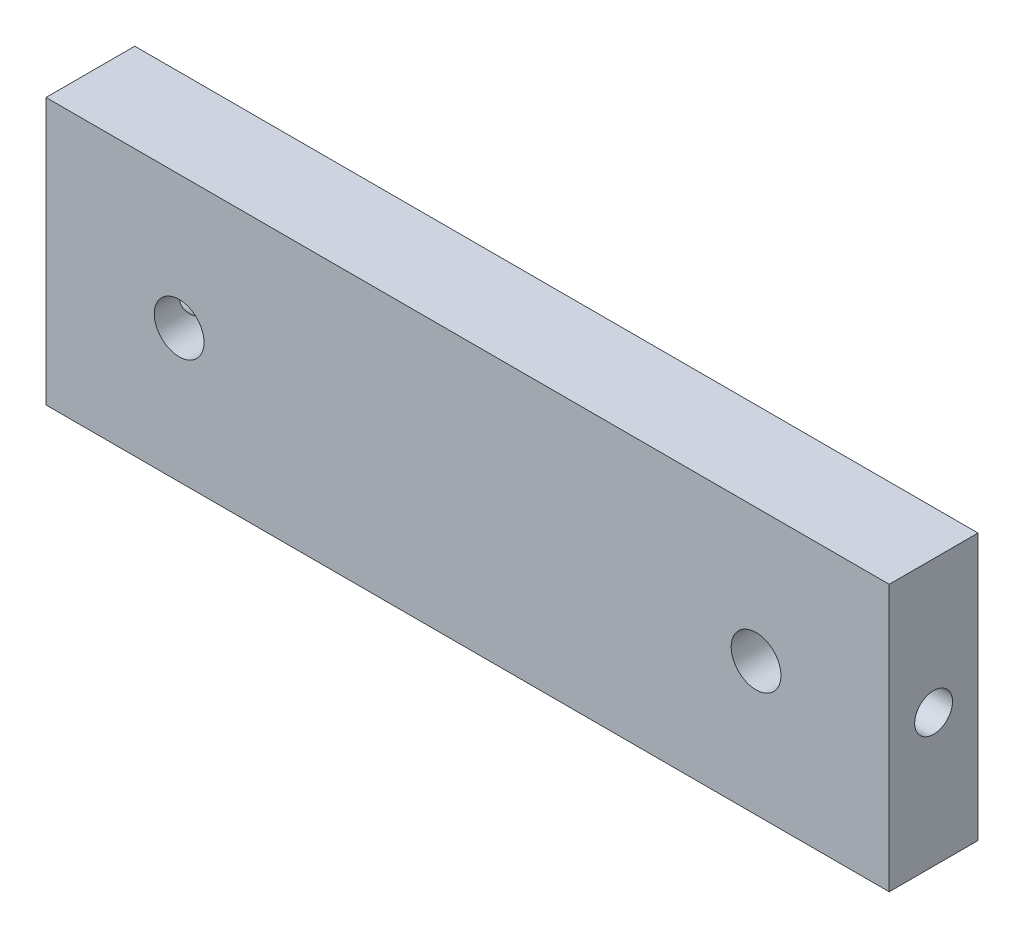
SolidWorks part; units mm, degrees
ref_plane "Front Plane" through (0, 0, 0) normal (0, 0, 1) x (1, 0, 0)
ref_plane "Top Plane" through (0, 0, 0) normal (0, 1, 0) x (1, 0, 0)
ref_plane "Right Plane" through (0, 0, 0) normal (1, 0, 0) x (0, 0, -1)
sketch "Sketch1" plane through (0, 0, 0) normal (0, 0, 1) x (1, 0, 0)
  line L1 (0, 0) -> (60.3123, 0)
  line L2 (0, 0) -> (0, 19.05)
  line L3 (0, 19.05) -> (60.3123, 19.05)
  line L4 (60.3123, 0) -> (60.3123, 19.05)
  dimension "D1" = 19.05
  dimension "D2" = 60.3123
extrude "Extrude1" add sketch "Sketch1" along normal blind 6.35
sketch "Sketch2" plane through (0, 0, 6.35) normal (0, 0, 1) x (1, 0, 0)
  line L0 (60.3123, 19.05) -> (0, 19.05) construction
  line L1 (60.3123, 0) -> (60.3123, 19.05) construction
  line L2 (0, 19.05) -> (0, 0) construction
  circle A0 centre (9.525, 9.525) radius 1.778
  circle A1 centre (50.7873, 9.525) radius 1.778
  dimension "D1" = 3.556
  dimension "D3" = 9.525
  dimension "D4" = 9.525
  dimension "D2" = 9.525
extrude "Cut-Extrude1" cut sketch "Sketch2" against normal through all
hole_wizard "#6-32 Tapped Hole1" positions "Sketch4" profile "Sketch3" tap size "#6-32" standard "Ansi Inch"
sketch "Sketch4" plane through (0, 0, 0) normal (-1, 0, 0) x (0, 0, 1)
  line L0 (6.35, 19.05) -> (0, 19.05) construction
  line L2 (6.35, 19.05) -> (6.35, 0) construction
  point P0 (3.175, 9.525)
  dimension "D1" = 9.525
  dimension "D2" = 3.175
sketch "Sketch3" plane through (0, 9.525, 3.175) normal (0, 1, 0) x (0, 0, 1)
  line L0 (0, 0) -> (0, 10.3377)
  line L1 (0, 10.3377) -> (1.3525, 9.525)
  line L2 (1.3525, 9.525) -> (1.3525, 0)
  line L5 (1.3525, 0) -> (0, 0)
  line L10 (0, 10.3377) -> (-1.3526, 9.525) construction
  line L11 (0, -6.35) -> (0, 107.95) construction
  dimension "Tap Drill Dia." = 2.7051
  dimension "Tap Drill Depth" = 9.525
  dimension "Drill Angle" = 118
cosmetic thread "Hole Thread1" parameters "D1"=7.0104, "D2"=3.5052
hole_wizard "#6-32 Tapped Hole2" positions "Sketch6" profile "Sketch5" tap size "#6-32" standard "Ansi Inch"
sketch "Sketch6" plane through (60.3123, 0, 0) normal (1, 0, 0) x (0, 0, -1)
  line L0 (-6.35, 19.05) -> (0, 19.05) construction
  line L1 (-6.35, 0) -> (-6.35, 19.05) construction
  point P0 (-3.175, 9.525)
  dimension "D1" = 9.525
  dimension "D2" = 3.175
sketch "Sketch5" plane through (60.3123, 9.525, 3.175) normal (0, 1, 0) x (0, 0, -1)
  line L0 (0, 0) -> (0, 10.3377)
  line L1 (0, 10.3377) -> (1.3525, 9.525)
  line L2 (1.3525, 9.525) -> (1.3525, 0)
  line L5 (1.3525, 0) -> (0, 0)
  line L10 (0, 10.3377) -> (-1.3525, 9.525) construction
  line L11 (0, -6.35) -> (0, 107.95) construction
  dimension "Tap Drill Dia." = 2.7051
  dimension "Tap Drill Depth" = 9.525
  dimension "Drill Angle" = 118
cosmetic thread "Hole Thread2" parameters "D1"=7.0104, "D2"=3.5052
